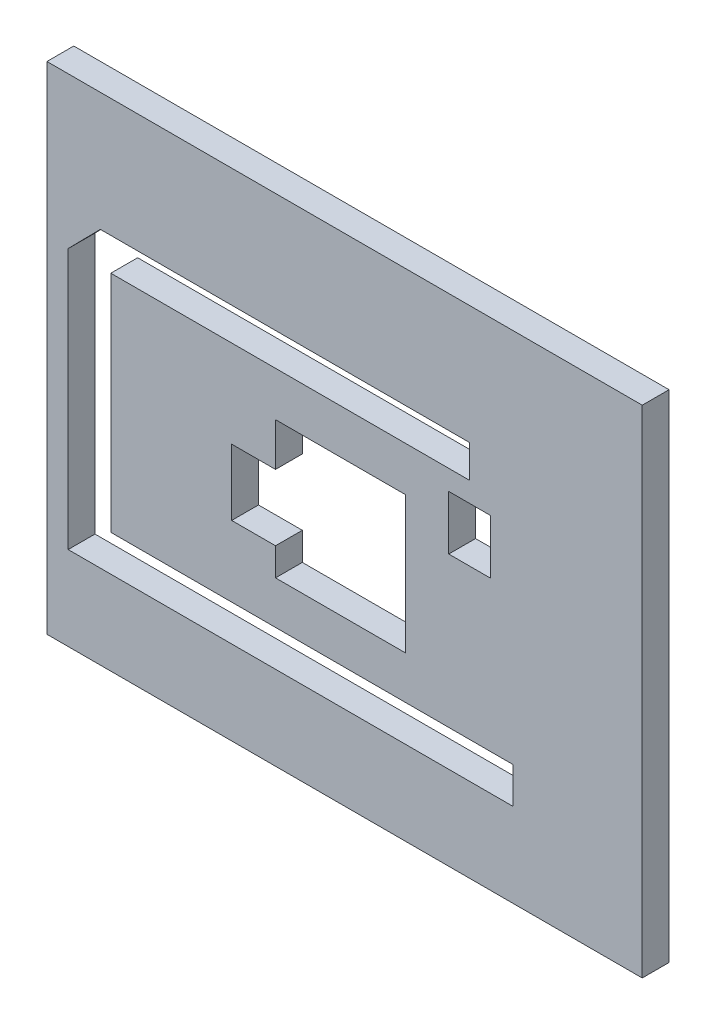
SolidWorks part; units mm, degrees
ref_plane "Alzado" through (0, 0, 0) normal (0, 0, 1) x (1, 0, 0)
ref_plane "Planta" through (0, 0, 0) normal (0, 1, 0) x (1, 0, 0)
ref_plane "Vista lateral" through (0, 0, 0) normal (1, 0, 0) x (0, 0, -1)
sketch "Croquis1" plane through (0, 0, 0) normal (0, 0, 1) x (1, 0, 0)
  line L0 (-1.3399, 59.6009) -> (4.6535, 65.7033)
  line L2 (-1.3399, 59.6009) -> (-1.3399, 11)
  line L3 (-1.3399, 11) -> (6.615, 11)
  line L4 (6.615, 59.6009) -> (6.615, 17.7562)
  line L5 (4.6535, 65.7033) -> (73.523, 65.7033)
  line L7 (6.615, 59.6009) -> (73.523, 59.6009)
  line L8 (73.523, 65.7033) -> (73.523, 59.6009)
  line L9 (6.615, 17.7562) -> (81.5868, 17.7562)
  line L11 (6.615, 11) -> (81.5868, 11)
  line L12 (81.5868, 17.7562) -> (81.5868, 11)
  line L13 (29.1519, 43.2685) -> (37.3244, 43.2685)
  line L14 (29.1519, 43.2685) -> (29.1519, 30.945)
  line L15 (29.1519, 30.945) -> (37.3244, 30.945)
  line L17 (69.6249, 55.8744) -> (77.4081, 55.8744)
  line L18 (69.6249, 55.8744) -> (69.6249, 45.7562)
  line L19 (69.6249, 45.7562) -> (77.4081, 45.7562)
  line L20 (77.4081, 55.8744) -> (77.4081, 45.7562)
  line L21 (37.3244, 51.3112) -> (61.5822, 51.3112)
  line L22 (37.3244, 51.3112) -> (37.3244, 43.2685)
  line L23 (37.3244, 25.7562) -> (61.5822, 25.7562)
  line L24 (61.5822, 51.3112) -> (61.5822, 25.7562)
  line L25 (-5.2944, 81.8357) -> (-5.2944, -4.6643)
  line L26 (-5.2944, -4.6643) -> (105.7056, -4.6643)
  line L27 (105.7056, -4.6643) -> (105.7056, 81.8357)
  line L28 (105.7056, 81.8357) -> (-5.2944, 81.8357)
  line L29 (37.3244, 30.945) -> (37.3244, 25.7562)
  dimension "D1" = 86.5
  dimension "D2" = 111
  dimension "D3" = 6.7562
  dimension "D4" = 6.1024
  dimension "D5" = 10.1182
  dimension "D6" = 7.7833
  dimension "D7" = 82.9267
  dimension "D8" = 74.8629
  dimension "D9" = 45.516
  dimension "D10" = 41.8448
  dimension "D11" = 32.4302
  dimension "D12" = 24.2578
  dimension "D13" = 5.1888
  dimension "D14" = 12.3235
  dimension "D15" = 4.6535
  dimension "D16" = 6.615
  dimension "D17" = 29.1519
  dimension "D18" = 11
  dimension "D19" = 69.6249
  dimension "D20" = 8
  dimension "D21" = 25.555
  dimension "D22" = 105.7056
  dimension "D23" = 28
  dimension "D24" = 81.8357
extrude "Saliente-Extruir1" add sketch "Croquis1" along normal blind 5
sketch "Croquis2" plane through (0, 0, 5) normal (0, 0, 1) x (1, 0, 0)
  line L0 (81.5868, 11) -> (81.5868, 17.7562) construction
  line L1 (81.5868, 17.7562) -> (6.615, 17.7562) construction
  line L2 (-1.3399, 11) -> (81.5868, 11) construction
  line L3 (-1.3399, 59.6009) -> (-1.3399, 11) construction
  line L4 (105.7056, 81.8357) -> (-5.2944, 81.8357)
  line L5 (-5.2944, 81.8357) -> (-5.2944, -4.6643)
  line L6 (-5.2944, -4.6643) -> (105.7056, -4.6643)
  line L7 (105.7056, -4.6643) -> (105.7056, 81.8357)
  line L8 (105.7056, 81.8357) -> (-5.2944, 81.8357)
  line L9 (-5.2944, 81.8357) -> (-5.2944, -4.6643)
  line L10 (-5.2944, -4.6643) -> (105.7056, -4.6643)
  line L11 (105.7056, -4.6643) -> (105.7056, 81.8357)
  line L12 (6.615, 17.7562) -> (6.615, 59.6009) construction
  line L13 (4.6535, 65.7033) -> (-1.3399, 59.6009) construction
  line L14 (73.523, 59.6009) -> (73.523, 65.7033) construction
  line L15 (73.523, 65.7033) -> (4.6535, 65.7033) construction
  line L16 (6.615, 59.6009) -> (73.523, 59.6009) construction
  line L17 (61.5822, 51.3112) -> (37.3244, 51.3112) construction
  line L18 (37.3244, 51.3112) -> (37.3244, 43.2685) construction
  line L19 (37.3244, 43.2685) -> (29.1519, 43.2685) construction
  line L20 (29.1519, 43.2685) -> (29.1519, 30.945) construction
  line L21 (29.1519, 30.945) -> (37.3244, 30.945) construction
  line L22 (37.3244, 30.945) -> (37.3244, 25.7562) construction
  line L23 (37.3244, 25.7562) -> (61.5822, 25.7562) construction
  line L24 (61.5822, 25.7562) -> (61.5822, 51.3112) construction
  line L25 (77.4081, 45.7562) -> (77.4081, 55.8744) construction
  line L26 (69.6249, 45.7562) -> (77.4081, 45.7562) construction
  line L27 (69.6249, 55.8744) -> (69.6249, 45.7562) construction
  line L28 (77.4081, 55.8744) -> (69.6249, 55.8744) construction
  line L29 (81.5868, 11) -> (81.5868, 17.7562)
  line L30 (81.5868, 17.7562) -> (6.615, 17.7562)
  line L31 (-1.3399, 11) -> (81.5868, 11)
  line L32 (-1.3399, 59.6009) -> (-1.3399, 11)
  line L33 (6.615, 17.7562) -> (6.615, 59.6009)
  line L34 (4.6535, 65.7033) -> (-1.3399, 59.6009)
  line L35 (73.523, 59.6009) -> (73.523, 65.7033)
  line L36 (73.523, 65.7033) -> (4.6535, 65.7033)
  line L37 (6.615, 59.6009) -> (73.523, 59.6009)
  line L38 (61.5822, 51.3112) -> (37.3244, 51.3112)
  line L39 (37.3244, 51.3112) -> (37.3244, 43.2685)
  line L40 (37.3244, 43.2685) -> (29.1519, 43.2685)
  line L41 (29.1519, 43.2685) -> (29.1519, 30.945)
  line L42 (29.1519, 30.945) -> (37.3244, 30.945)
  line L43 (37.3244, 30.945) -> (37.3244, 25.7562)
  line L44 (37.3244, 25.7562) -> (61.5822, 25.7562)
  line L45 (61.5822, 25.7562) -> (61.5822, 51.3112)
  line L46 (77.4081, 45.7562) -> (77.4081, 55.8744)
  line L47 (69.6249, 45.7562) -> (77.4081, 45.7562)
  line L48 (69.6249, 55.8744) -> (69.6249, 45.7562)
  line L49 (77.4081, 55.8744) -> (69.6249, 55.8744)
  dimension "D1" = 0
sketch "Croquis3" plane through (0, 81.8357, 0) normal (0, 1, 0) x (1, 0, 0)
  line L4 (105.7056, 0) -> (-5.2944, 0)
  line L5 (-5.2944, 0) -> (-5.2944, -5)
  line L6 (-5.2944, -5) -> (105.7056, -5)
  line L7 (105.7056, -5) -> (105.7056, 0)
  line L8 (105.7056, 0) -> (-5.2944, 0)
  line L9 (-5.2944, 0) -> (-5.2944, -5)
  line L10 (-5.2944, -5) -> (105.7056, -5)
  line L11 (105.7056, -5) -> (105.7056, 0)
  dimension "D1" = 0
extrude "Saliente-Extruir2" add sketch "Croquis3" along normal blind 6
